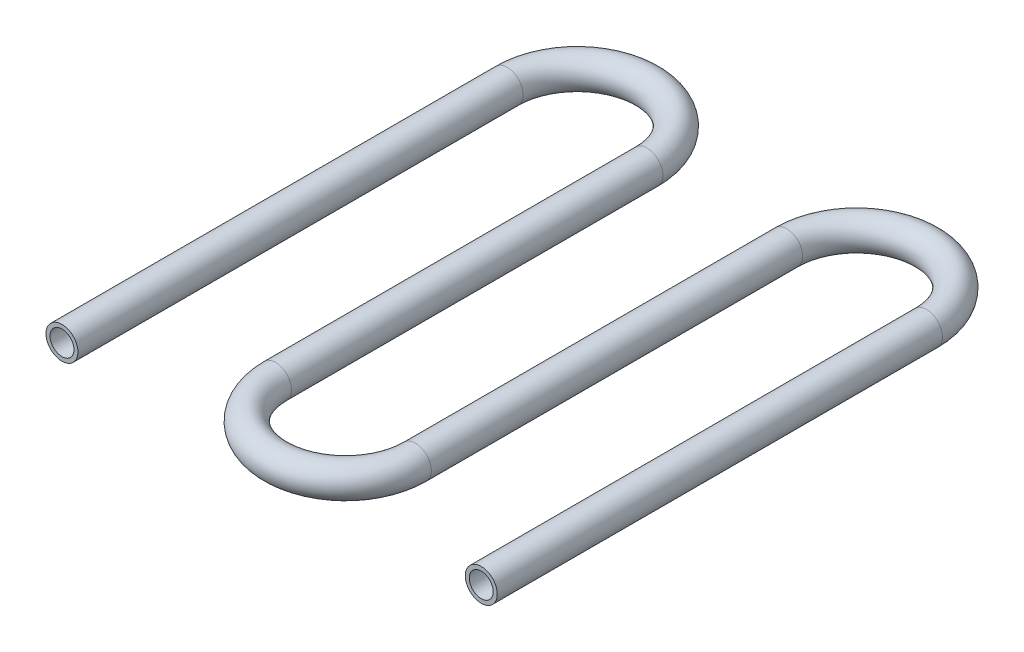
SolidWorks part; units mm, degrees
ref_plane "Front Plane" through (0, 0, 0) normal (0, 0, 1) x (1, 0, 0)
ref_plane "Top Plane" through (0, 0, 0) normal (0, 1, 0) x (1, 0, 0)
ref_plane "Right Plane" through (0, 0, 0) normal (1, 0, 0) x (0, 0, -1)
sketch "Sketch1" plane through (0, 0, 0) normal (0, 1, 0) x (1, 0, 0)
  line L0 (0, -46.5) -> (0, 46.5) construction
  line L1 (-17.5, -46.5) -> (-17.5, 46.5)
  line L2 (17.5, -46.5) -> (17.5, 46.5)
  line L3 (35, 46.5) -> (35, -46.5) construction
  line L4 (52.5, 46.5) -> (52.5, -46.5)
  line L5 (17.5, 46.5) -> (17.5, -46.5)
  line L6 (70, 46.5) -> (70, -46.5) construction
  line L7 (87.5, 46.5) -> (87.5, -46.5)
  line L8 (52.5, 46.5) -> (52.5, -46.5)
  arc A0 (-17.5, -46.5) -> (17.5, -46.5) centre (0, -46.5) ccw
  arc A1 (17.5, 46.5) -> (-17.5, 46.5) centre (0, 46.5) ccw
  arc A2 (52.5, 46.5) -> (17.5, 46.5) centre (35, 46.5) ccw
  arc A3 (17.5, -46.5) -> (52.5, -46.5) centre (35, -46.5) ccw
  arc A4 (87.5, 46.5) -> (52.5, 46.5) centre (70, 46.5) ccw
  arc A5 (52.5, -46.5) -> (87.5, -46.5) centre (70, -46.5) ccw
  point P2 (0, 0)
  point P10 (35, 0)
  point P16 (70, 0)
  point P22 (0, 0)
  dimension "D1" = 128
  dimension "D2" = 35
sketch "Sketch2" plane through (0, 0, 0) normal (0, 1, 0) x (1, 0, 0)
  line L0 (87.5, 46.5) -> (87.5, -46.5) construction
  line L1 (52.5, 46.5) -> (52.5, -46.5) construction
  line L2 (17.5, -46.5) -> (17.5, 46.5) construction
  line L3 (-17.5, -46.5) -> (-17.5, 46.5) construction
  line L4 (87.5, 46.5) -> (87.5, -65)
  line L5 (52.5, 46.5) -> (52.5, -46.5)
  line L6 (17.5, -46.5) -> (17.5, 46.5)
  line L7 (-17.5, -65) -> (-17.5, 46.5)
  arc A0 (87.5, 46.5) -> (52.5, 46.5) centre (70, 46.5) ccw construction
  arc A1 (17.5, -46.5) -> (52.5, -46.5) centre (35, -46.5) ccw construction
  arc A2 (17.5, 46.5) -> (-17.5, 46.5) centre (0, 46.5) ccw construction
  arc A3 (87.5, 46.5) -> (52.5, 46.5) centre (70, 46.5) ccw
  arc A4 (17.5, -46.5) -> (52.5, -46.5) centre (35, -46.5) ccw
  arc A5 (17.5, 46.5) -> (-17.5, 46.5) centre (0, 46.5) ccw
  point P9 (0, 0)
  dimension "D1" = 65
ref_plane "Plane1" through (0, 0, 65) normal (0, 0, 1) x (1, 0, 0)
sketch "Sketch3" plane through (0, 0, 65) normal (0, 0, 1) x (1, 0, 0)
  circle A0 centre (-17.5, 0) radius 4
  circle A1 centre (-17.5, 0) radius 3
  dimension "D1" = 8
  dimension "D2" = 1
sweep "Sweep1" add profiles "Sketch3" path "Sketch2"
ref_plane "Plane2" through (35, 0, 0) normal (1, 0, 0) x (0, 0, -1)
